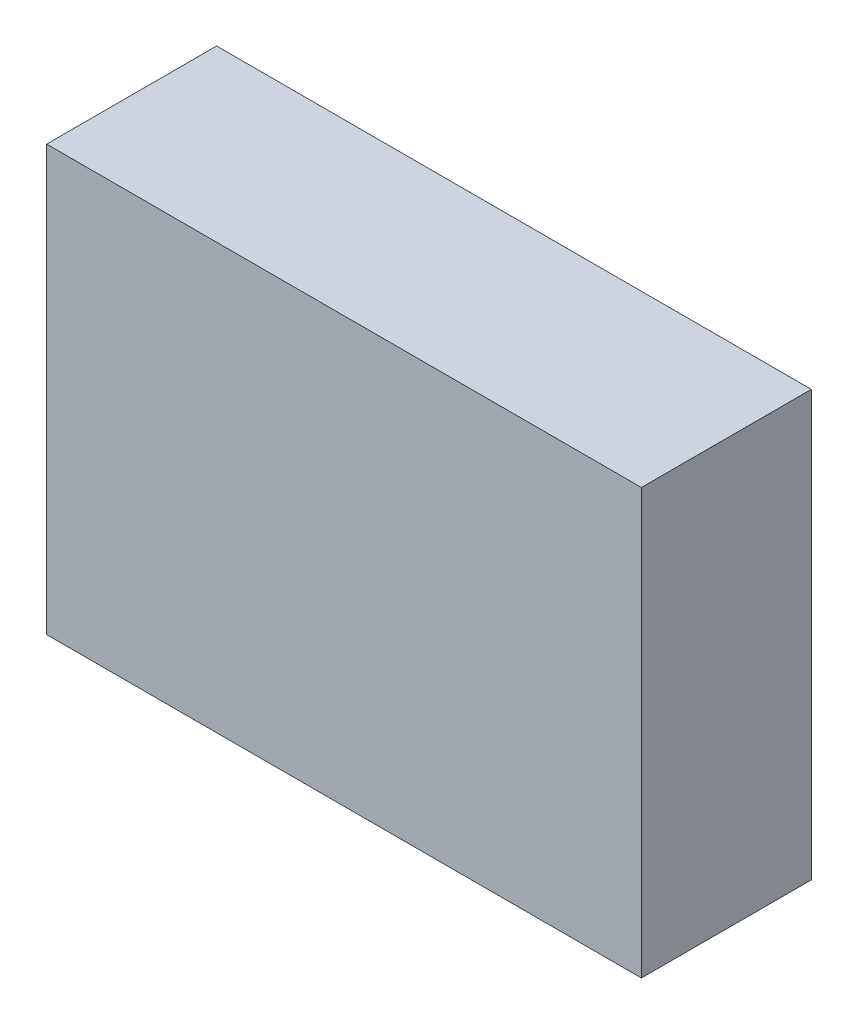
SolidWorks part; units mm, degrees
ref_plane "Front Plane" through (0, 0, 0) normal (0, 0, 1) x (1, 0, 0)
ref_plane "Top Plane" through (0, 0, 0) normal (0, 1, 0) x (1, 0, 0)
ref_plane "Right Plane" through (0, 0, 0) normal (1, 0, 0) x (0, 0, -1)
sketch "Sketch1" plane through (0, 0, 0) normal (0, 0, 1) x (1, 0, 0)
  line L1 (-88.9, 63.5) -> (88.9, 63.5)
  line L2 (-88.9, 63.5) -> (-88.9, -63.5)
  line L3 (-88.9, -63.5) -> (88.9, -63.5)
  line L4 (88.9, 63.5) -> (88.9, -63.5)
  line L5 (-88.9, 63.5) -> (88.9, -63.5) construction
  line L6 (-88.9, -63.5) -> (88.9, 63.5) construction
  point P0 (0, 0)
  dimension "D1" = 177.8
  dimension "D2" = 127
extrude "Boss-Extrude1" add sketch "Sketch1" along normal blind 50.8
